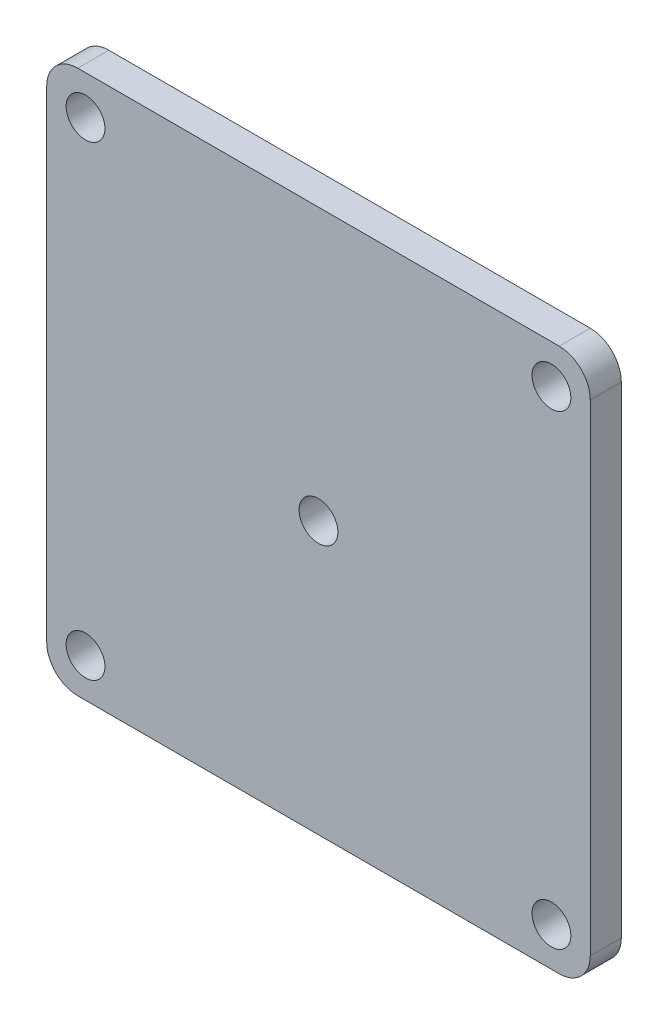
SolidWorks part; units mm, degrees
ref_plane "Front Plane" through (0, 0, 0) normal (0, 0, 1) x (1, 0, 0)
ref_plane "Top Plane" through (0, 0, 0) normal (0, 1, 0) x (1, 0, 0)
ref_plane "Right Plane" through (0, 0, 0) normal (1, 0, 0) x (0, 0, -1)
sketch "Sketch1" plane through (0, 0, 0) normal (0, 0, 1) x (1, 0, 0)
  line L1 (0, 0) -> (88.9, 0)
  line L2 (0, 0) -> (0, 88.9)
  line L3 (0, 88.9) -> (88.9, 88.9)
  line L4 (88.9, 0) -> (88.9, 88.9)
  dimension "D1" = 88.9
  dimension "D2" = 88.9
extrude "Boss-Extrude1" add sketch "Sketch1" along normal mid plane 5.08
sketch "Sketch2" plane through (0, 0, 2.54) normal (0, 0, 1) x (1, 0, 0)
  line L0 (44.45, 88.9) -> (44.45, 0) construction
  line L1 (82.55, 6.35) -> (6.35, 6.35) construction
  line L2 (82.55, 6.35) -> (82.55, 82.55) construction
  line L3 (82.55, 82.55) -> (6.35, 82.55) construction
  line L4 (6.35, 6.35) -> (6.35, 82.55) construction
  line L5 (82.55, 6.35) -> (6.35, 82.55) construction
  line L6 (82.55, 82.55) -> (6.35, 6.35) construction
  line L7 (88.9, 88.9) -> (0, 88.9) construction
  line L8 (0, 0) -> (88.9, 0) construction
  circle A0 centre (6.35, 82.55) radius 3.175
  circle A1 centre (82.55, 82.55) radius 3.175
  circle A2 centre (82.55, 6.35) radius 3.175
  circle A3 centre (6.35, 6.35) radius 3.175
  circle A4 centre (44.45, 44.45) radius 3.175
  point P0 (44.45, 44.45)
  point P12 (44.45, 44.45)
  dimension "D2" = 6.35
  dimension "D1" = 76.2
extrude "Cut-Extrude1" cut sketch "Sketch2" against normal through all
fillet "Fillet1" radius 5.08 4 edges at (88.9, 0, 0) (0, 0, 0) (88.9, 88.9, 0) (0, 88.9, 0)
